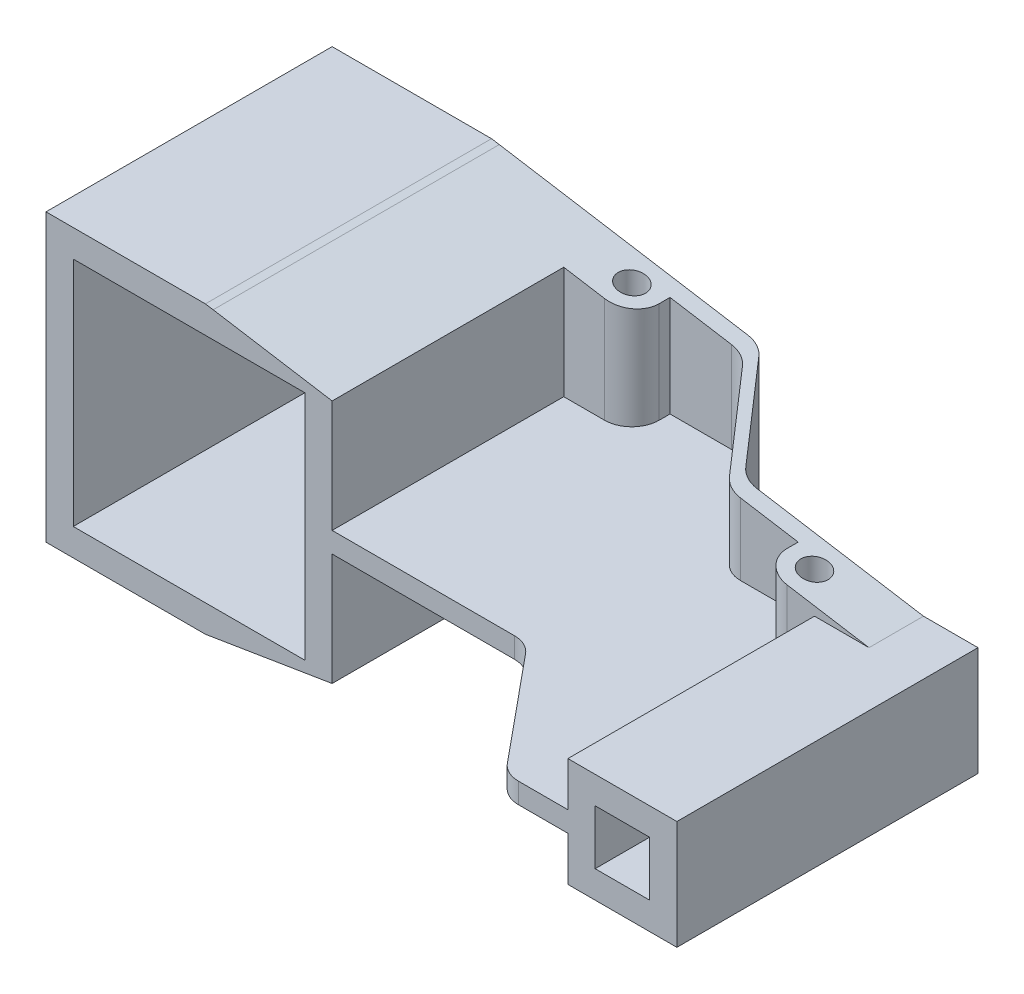
SolidWorks part; units mm, degrees
material "Alliage 1060"
ref_plane "Plan de face" through (0, 0, 0) normal (0, 0, 1) x (1, 0, 0)
ref_plane "Plan de dessus" through (0, 0, 0) normal (0, 1, 0) x (1, 0, 0)
ref_plane "Plan de droite" through (0, 0, 0) normal (1, 0, 0) x (0, 0, -1)
sketch "Esquisse1" plane through (0, 0, 0) normal (0, 0, 1) x (1, 0, 0)
  line L0 (-95.067, 52.5) -> (108.933, 20)
  line L1 (-143.567, -42.5) -> (-58.567, -42.5)
  line L2 (-143.567, -42.5) -> (-143.567, 42.5)
  line L3 (-143.567, 42.5) -> (-58.567, 42.5)
  line L4 (-58.567, -42.5) -> (-58.567, 42.5)
  line L5 (-143.567, -42.5) -> (-58.567, 42.5) construction
  line L6 (-143.567, 42.5) -> (-58.567, -42.5) construction
  line L7 (-153.567, -52.5) -> (-48.567, -52.5)
  line L8 (-153.567, -52.5) -> (-153.567, 52.5)
  line L9 (-153.567, 52.5) -> (-48.567, 52.5)
  line L10 (-48.567, -52.5) -> (-48.567, 52.5)
  line L11 (-153.567, -52.5) -> (-48.567, 52.5) construction
  line L12 (-153.567, 52.5) -> (-48.567, -52.5) construction
  line L13 (98.933, -10) -> (118.933, -10)
  line L14 (98.933, -10) -> (98.933, 10)
  line L15 (98.933, 10) -> (118.933, 10)
  line L16 (118.933, -10) -> (118.933, 10)
  line L17 (98.933, -10) -> (118.933, 10) construction
  line L18 (98.933, 10) -> (118.933, -10) construction
  line L19 (88.933, -20) -> (128.933, -20)
  line L20 (88.933, -20) -> (88.933, 20)
  line L21 (88.933, 20) -> (128.933, 20)
  line L22 (128.933, -20) -> (128.933, 20)
  line L23 (88.933, -20) -> (128.933, 20) construction
  line L24 (88.933, 20) -> (128.933, -20) construction
  line L25 (-95.067, -52.5) -> (108.933, -20)
  point P0 (-101.067, 0)
  point P5 (-101.067, 0)
  point P10 (108.933, 0)
  point P15 (108.933, 0)
  point P20 (-95.067, 52.5)
  point P21 (-95.067, -52.5)
extrude "Boss.-Extru.1" add sketch "Esquisse1" along normal blind 105 contours L7 L25 L10 L0 L9 L8 L4 L1 L2 L3
sketch "Esquisse2" plane through (0, -52.5, 0) normal (0, -1, 0) x (1, 0, 0)
  line L2 (-153.567, 105) -> (-153.567, 0) construction
  line L3 (-95.067, 0) -> (-48.567, 0) construction
  line L5 (-48.567, 0) -> (-23.567, 0)
  line L6 (-48.567, 0) -> (-48.567, 20)
  line L7 (-48.567, 20) -> (-23.567, 20)
  line L8 (-23.567, 0) -> (-23.567, 20)
  point P0 (-33.567, 10)
  dimension "D1" = 120
  dimension "D2" = 10
  dimension "D3" = 20
  dimension "D4" = 10
extrude "Boss.-Extru.2" add sketch "Esquisse2" against normal through all
sketch "Esquisse3" plane through (0, -52.5, 0) normal (0, -1, 0) x (1, 0, 0)
  circle A0 centre (-33.567, 10) radius 5
  point P0 (-33.567, 10)
  dimension "D1" = 10
extrude "Enlèv. mat.-Extru.1" cut sketch "Esquisse3" against normal through all
sketch "Esquisse5" plane through (0, 0, 105) normal (0, 0, 1) x (1, 0, 0)
  line L0 (-48.567, 45.0919) -> (-48.567, -45.0919) construction
  line L1 (-23.567, -52.5) -> (-48.567, -52.5) construction
  line L2 (-23.567, 52.5) -> (-48.567, 52.5) construction
  line L3 (-23.567, 52.5) -> (-23.567, -52.5) construction
  line L4 (-48.567, -3.75) -> (-23.567, -3.75)
  line L5 (-48.567, -3.75) -> (-48.567, 3.75)
  line L6 (-48.567, 3.75) -> (-23.567, 3.75)
  line L7 (-23.567, -3.75) -> (-23.567, 3.75)
  point P0 (-48.567, 3.75)
  point P1 (-48.567, -3.75)
  dimension "D1" = 48.75
  dimension "D2" = 48.75
extrude "Boss.-Extru.3" add sketch "Esquisse5" against normal up to next
fillet "Congé1" radius 10 2 edges at (-23.567, -28.125, 20) (-23.567, 28.125, 20)
sketch "Esquisse6" plane through (0, 0, 0) normal (0, 0, -1) x (-1, 0, 0)
  line L0 (58.567, 42.5) -> (143.567, -42.5)
  line L1 (-113.451, -10.0001) -> (-93.451, -10.0001)
  line L2 (-113.451, -10.0001) -> (-113.451, 10.0001)
  line L3 (-113.451, 10.0001) -> (-93.451, 10.0001)
  line L4 (-93.451, -10.0001) -> (-93.451, 10.0001)
  line L5 (-113.451, -10.0001) -> (-93.451, 10.0001) construction
  line L6 (-113.451, 10.0001) -> (-93.451, -10.0001) construction
  line L7 (-123.451, -20) -> (-83.451, -20)
  line L8 (-123.451, -20) -> (-123.451, 20)
  line L9 (-123.451, 20) -> (-83.451, 20)
  line L10 (-83.451, -20) -> (-83.451, 20)
  line L11 (-123.451, -20) -> (-83.451, 20) construction
  line L12 (-123.451, 20) -> (-83.451, -20) construction
  line L13 (58.567, -42.5) -> (58.567, 42.5) construction
  line L14 (143.567, 42.5) -> (58.567, 42.5) construction
  line L15 (143.567, -42.5) -> (143.567, 42.5)
  line L16 (143.567, 42.5) -> (58.567, -42.5)
  line L17 (143.567, -42.5) -> (58.567, -42.5) construction
  point P0 (-103.451, 0)
  point P5 (-103.451, 0)
  point P22 (101.067, 0)
  dimension "D6" = 0
extrude "Boss.-Extru.5" add sketch "Esquisse6" against normal blind 176 and the other way blind 83 separate body contours L7 L10 L9 L8 L4 L1 L2 L3
sketch "Esquisse7" plane through (0, -52.5, 0) normal (0, -1, 0) x (1, 0, 0)
  line L1 (-23.567, 0) -> (143.2056, 0)
  line L2 (-23.567, 0) -> (-23.567, 40)
  line L3 (-23.567, 40) -> (143.2056, 40)
  line L4 (143.2056, 0) -> (143.2056, 40)
  line L5 (75.7227, 40) -> (143.2056, 40)
  line L6 (75.7227, 40) -> (75.7227, -90.2735)
  line L7 (75.7227, -90.2735) -> (143.2056, -90.2735)
  line L8 (143.2056, 40) -> (143.2056, -90.2735)
  dimension "D1" = 40
extrude "Enlèv. mat.-Extru.2" cut sketch "Esquisse7" against normal through all contours L8 L1 L6 L7 | L3 L6 L1 L4
sketch "Esquisse8" plane through (0, -20, 0) normal (0, -1, 0) x (1, 0, 0)
  line L0 (123.451, 40) -> (123.451, 176) construction
  line L1 (83.451, 40) -> (123.451, 40)
  line L2 (83.451, 40) -> (83.451, 150.5)
  line L3 (83.451, 150.5) -> (123.451, 150.5)
  line L4 (123.451, 40) -> (123.451, 150.5)
  line L6 (83.451, 150.5) -> (123.451, 150.5)
  line L7 (83.451, 150.5) -> (83.451, 187.4298)
  line L8 (83.451, 187.4298) -> (123.451, 187.4298)
  line L9 (123.451, 150.5) -> (123.451, 187.4298)
  line M3 (123.451, 40) -> (123.451, 176)
  line M4 (123.451, 176) -> (83.451, 176)
  line M5 (83.451, 176) -> (83.451, 40)
  dimension "D1" = 110.5
extrude "Enlèv. mat.-Extru.3" cut sketch "Esquisse8" against normal through all contours L3 M5 M3 M4
sketch "Esquisse9" plane through (0, -20, 0) normal (0, -1, 0) x (-1, 0, 0)
  line L1 (-123.451, -40) -> (-83.451, -40) construction
  line L3 (-83.451, -40) -> (-63.451, -40)
  line L4 (-83.451, -40) -> (-83.451, -60)
  line L5 (-83.451, -60) -> (-63.451, -60)
  line L6 (-63.451, -40) -> (-63.451, -60)
  point P0 (-73.451, -50)
  dimension "D1" = 50
  dimension "D2" = 10
  dimension "D3" = 20
  dimension "D4" = 10
extrude "Boss.-Extru.7" add sketch "Esquisse9" against normal blind 40
sketch "Esquisse11" plane through (0, -52.5, 0) normal (0, -1, 0) x (1, 0, 0)
  line L0 (123.451, 40) -> (63.451, 40) construction
  line L2 (103.7929, 40) -> (63.451, 40)
  line L3 (103.7929, 40) -> (103.7929, 60)
  line L4 (103.7929, 60) -> (63.451, 60)
  line L5 (63.451, 40) -> (63.451, 60)
  point P0 (103.7929, 40)
extrude "Boss.-Extru.8" add sketch "Esquisse11" against normal up to next (32.5 mm away)
sketch "Esquisse12" plane through (0, 52.5, 0) normal (0, 1, 0) x (1, 0, 0)
  line L0 (123.451, -40) -> (63.451, -40) construction
  line L1 (123.451, -40) -> (123.451, -150.5) construction
  line L2 (63.451, -60) -> (63.451, -40) construction
  line L3 (103.451, -40) -> (63.451, -40)
  line L4 (103.451, -40) -> (103.451, -60)
  line L5 (103.451, -60) -> (63.451, -60)
  line L6 (63.451, -40) -> (63.451, -60)
  line L7 (83.451, -60) -> (63.451, -60) construction
  point P0 (103.451, -40)
  dimension "D1" = 20
extrude "Boss.-Extru.9" add sketch "Esquisse12" against normal up to next (32.5 mm away)
sketch "Esquisse13" plane through (0, -52.5, 0) normal (0, -1, 0) x (1, 0, 0)
  line L0 (63.451, 40) -> (103.7929, 40) construction
  circle A0 centre (73.451, 50) radius 5
  point P0 (73.451, 50)
  dimension "D3" = 10
  dimension "D1" = 50
  dimension "D2" = 10
extrude "Enlèv. mat.-Extru.4" cut sketch "Esquisse13" against normal through all
sketch "Esquisse14" plane through (0, -52.5, 0) normal (0, -1, 0) x (1, 0, 0)
  line L0 (-23.567, 0) -> (-1.0741, 0)
  line L1 (-1.0741, 6) -> (-23.567, 6)
  line L2 (63.451, 40) -> (42.3351, 40)
  line L3 (34.7339, 42.4979) -> (6.527, 9.5021)
  line L4 (42.3351, 46) -> (63.451, 46)
  line L5 (63.451, 60) -> (63.451, 40) construction
  line L6 (63.451, 46) -> (63.451, 40)
  line L7 (34.7339, 36.4979) -> (6.527, 3.5021)
  line L8 (-23.567, 0) -> (-23.567, 10) construction
  line L9 (-23.567, 6) -> (-23.567, 0)
  arc A0 (42.3351, 40) -> (34.7339, 36.4979) centre (42.3351, 30) ccw
  arc A1 (6.527, 3.5021) -> (-1.0741, 0) centre (-1.0741, 10) cw
  arc A2 (6.527, 9.5021) -> (-1.0741, 6) centre (-1.0741, 16) cw
  arc A3 (34.7339, 42.4979) -> (42.3351, 46) centre (42.3351, 36) cw
  point P4 (60.9668, 6)
  point P24 (0, 0)
extrude "Boss.-Extru.11" add sketch "Esquisse14" against normal through all
sketch "Esquisse15" plane through (0, 0, 150.5) normal (0, 0, 1) x (1, 0, 0)
  line L0 (83.451, 20) -> (83.451, -20) construction
  line L1 (-23.567, 3.75) -> (83.451, 3.75)
  line L2 (-23.567, 3.75) -> (-23.567, -3.75)
  line L3 (-23.567, -3.75) -> (83.451, -3.75)
  line L4 (83.451, 3.75) -> (83.451, -3.75)
extrude "Boss.-Extru.12" add sketch "Esquisse15" against normal up to next
fillet "Congé2" radius 10 1 edges at (63.451, -28.125, 60)
fillet "Congé3" radius 10 1 edges at (63.451, 28.125, 60)
sketch "Esquisse16" plane through (0, -3.75, 0) normal (0, -1, 0) x (1, 0, 0)
  line L0 (60.5989, 150.5) -> (26.0695, 108.637)
  line L2 (-23.567, 105) -> (18.3551, 105)
  line L4 (-23.567, 105) -> (-23.567, 150.5)
  line L5 (-23.567, 105) -> (-23.567, 150.5) construction
  line L6 (-23.567, 150.5) -> (60.5989, 150.5)
  line L7 (-23.567, 150.5) -> (83.451, 150.5) construction
  arc A0 (18.3551, 105) -> (26.0695, 108.637) centre (18.3551, 115) ccw
  point P0 (-8.6501, 66.5433)
  dimension "D1" = 10
extrude "Enlèv. mat.-Extru.6" cut sketch "Esquisse16" against normal through all contours L2 A0 L0 L6 L4
fillet "Congé4" radius 10 1 edges at (60.5989, 0, 150.5)
sketch "Esquisse17" plane through (0, 0, 150.5) normal (0, 0, 1) x (1, 0, 0)
  line L0 (-93.4664, -52.245) -> (103.7929, -20)
  line L1 (-95.067, -52.5) -> (-48.567, -45.0919) construction
  line L2 (83.451, -20) -> (123.451, -20) construction
  line L3 (103.7929, -20) -> (83.451, -20) construction
  line L4 (103.7929, -20) -> (103.7929, -55.2756)
  line L5 (103.7929, -55.2756) -> (-93.4664, -52.245)
extrude "Enlèv. mat.-Extru.7" cut sketch "Esquisse17" against normal through all
sketch "Esquisse18" plane through (0, 0, 150.5) normal (0, 0, 1) x (1, 0, 0)
  line L0 (-92.2229, 52.0469) -> (103.451, 20)
  line L1 (-95.067, 52.5) -> (-48.567, 45.0919) construction
  line L2 (123.451, 20) -> (83.451, 20) construction
  line L3 (103.451, 20) -> (103.451, 52.5)
  line L4 (103.451, 52.5) -> (-92.2229, 52.0469)
extrude "Enlèv. mat.-Extru.8" cut sketch "Esquisse18" against normal through all
sketch "Esquisse19" plane through (0, 0, 150.5) normal (0, 0, 1) x (1, 0, 0)
  line L0 (-79.4632, 79.1786) -> (139.9794, 56.9356)
  line L1 (139.9794, 56.9356) -> (111.2411, 33.487)
  line L2 (111.2411, 33.487) -> (-48.9206, 47.64)
  line L3 (-48.9206, 47.64) -> (-79.4632, 79.1786)
extrude "Enlèv. mat.-Extru.9" cut sketch "Esquisse19" against normal through all
